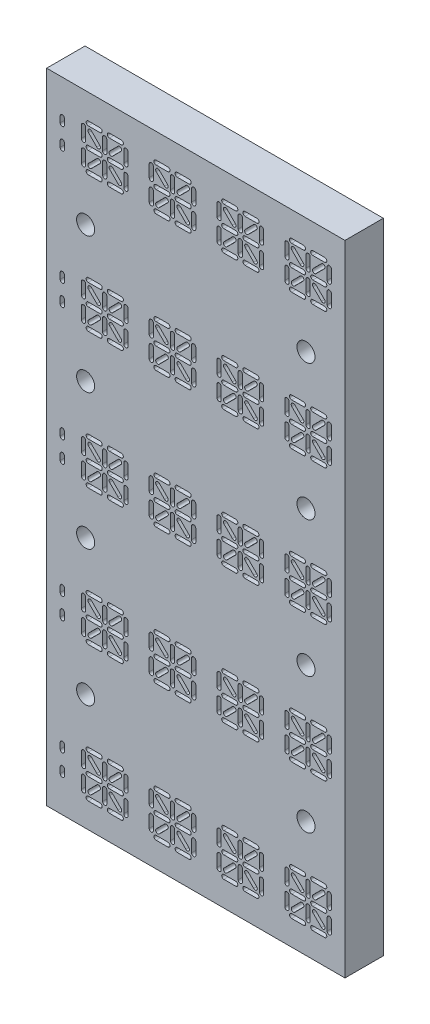
SolidWorks part; units mm, degrees
material "ABS PC"
ref_plane "Front Plane" through (0, 0, 0) normal (0, 0, 1) x (1, 0, 0)
ref_plane "Top Plane" through (0, 0, 0) normal (0, 1, 0) x (1, 0, 0)
ref_plane "Right Plane" through (0, 0, 0) normal (1, 0, 0) x (0, 0, -1)
sketch "Sketch1" plane through (0, 0, 0) normal (0, 0, 1) x (1, 0, 0)
  line L0 (265.9975, 197.0179) -> (342.1693, 194.9479) construction
  line L1 (297.418, 228.3826) -> (298.307, 228.3826) construction
  line L2 (297.418, 228.3826) -> (300.593, 228.3826) construction
  line L3 (302.371, 228.3826) -> (302.371, 231.5576) construction
  line L4 (296.7097, 229.0811) -> (296.7097, 229.9701) construction
  line L5 (296.7097, 230.8591) -> (296.7097, 234.0341) construction
  line L6 (296.7097, 234.0341) -> (299.8847, 234.0341) construction
  line L7 (296.7097, 234.0341) -> (297.0639, 234.3834) construction
  line L8 (296.7097, 234.0341) -> (297.418, 234.7326) construction
  line L9 (299.196, 231.5576) -> (300.593, 231.5576) construction
  line L10 (297.0639, 234.3834) -> (299.5404, 231.9069) construction
  line L11 (296.7097, 232.2561) -> (296.7097, 230.8591) construction
  line L12 (297.418, 231.5576) -> (296.7097, 231.5576) construction
  line L13 (299.8847, 232.2561) -> (299.196, 231.5576) construction
  line L14 (299.8945, 231.5576) -> (298.9307, 232.5165) construction
  line L15 (299.8945, 231.5576) -> (300.8534, 232.5214) construction
  line L16 (297.418, 234.7326) -> (307.578, 234.7326) construction
  line L17 (293.5347, 230.4146) -> (293.5347, 229.5256) construction
  line L18 (293.5347, 232.7006) -> (293.5347, 230.4146) construction
  line L19 (335.8892, 225.6039) -> (291.1852, 225.6039)
  line L20 (335.8892, 225.6039) -> (335.8892, 237.5114)
  line L21 (335.8892, 237.5114) -> (291.1852, 237.5114)
  line L22 (291.1852, 225.6039) -> (291.1852, 237.5114)
  line L23 (335.8892, 225.6039) -> (291.1852, 237.5114) construction
  line L24 (335.8892, 237.5114) -> (291.1852, 225.6039) construction
  line L25 (333.5397, 232.2561) -> (333.5397, 230.8591) construction
  line L26 (293.5347, 231.5576) -> (333.5397, 231.5576) construction
  line L27 (297.418, 228.3826) -> (299.196, 228.3826) construction
  line L32 (297.418, 228.7001) -> (299.196, 228.7001)
  line L33 (297.418, 228.0651) -> (299.196, 228.0651)
  line L34 (300.593, 228.3826) -> (302.371, 228.3826) construction
  line L35 (300.593, 228.7001) -> (302.371, 228.7001)
  line L36 (300.593, 228.0651) -> (302.371, 228.0651)
  line L37 (302.1155, 229.3415) -> (300.8582, 230.5987) construction
  line L38 (301.891, 229.117) -> (300.6337, 230.3742)
  line L39 (302.34, 229.566) -> (301.0827, 230.8233)
  line L40 (299.8847, 229.0811) -> (299.8847, 230.8591) construction
  line L41 (299.5672, 229.0811) -> (299.5672, 230.8591)
  line L42 (300.2022, 229.0811) -> (300.2022, 230.8591)
  line L43 (298.9356, 230.5939) -> (297.6784, 229.3366) construction
  line L44 (299.1601, 230.3694) -> (297.9029, 229.1121)
  line L45 (298.7111, 230.8184) -> (297.4539, 229.5611)
  line L46 (296.7097, 229.0811) -> (296.7097, 230.8591) construction
  line L47 (296.3922, 229.0811) -> (296.3922, 230.8591)
  line L48 (297.0272, 229.0811) -> (297.0272, 230.8591)
  line L49 (303.0597, 230.8591) -> (303.0597, 229.0811) construction
  line L50 (303.3772, 230.8591) -> (303.3772, 229.0811)
  line L51 (302.7422, 230.8591) -> (302.7422, 229.0811)
  line L52 (302.371, 231.5576) -> (300.593, 231.5576) construction
  line L53 (302.371, 231.2401) -> (300.593, 231.2401)
  line L54 (302.371, 231.8751) -> (300.593, 231.8751)
  line L55 (303.0597, 234.0341) -> (303.0597, 232.2561) construction
  line L56 (303.3772, 234.0341) -> (303.3772, 232.2561)
  line L57 (302.7422, 234.0341) -> (302.7422, 232.2561)
  line L58 (302.1106, 233.7786) -> (300.8534, 232.5214) construction
  line L59 (302.3351, 233.5541) -> (301.0779, 232.2969)
  line L60 (301.8861, 234.0031) -> (300.6289, 232.7459)
  line L61 (302.371, 234.7326) -> (300.593, 234.7326) construction
  line L62 (302.371, 234.4151) -> (300.593, 234.4151)
  line L63 (302.371, 235.0501) -> (300.593, 235.0501)
  line L64 (299.8847, 234.0341) -> (299.8847, 232.2561) construction
  line L65 (300.2022, 234.0341) -> (300.2022, 232.2561)
  line L66 (299.5672, 234.0341) -> (299.5672, 232.2561)
  line L67 (297.418, 231.5576) -> (299.196, 231.5576) construction
  line L68 (297.418, 231.8751) -> (299.196, 231.8751)
  line L69 (297.418, 231.2401) -> (299.196, 231.2401)
  line L70 (298.9307, 232.5165) -> (297.6735, 233.7737) construction
  line L71 (298.7062, 232.292) -> (297.449, 233.5492)
  line L72 (299.1552, 232.741) -> (297.898, 233.9983)
  line L73 (296.7097, 232.2561) -> (296.7097, 234.0341) construction
  line L74 (296.3922, 232.2561) -> (296.3922, 234.0341)
  line L75 (297.0272, 232.2561) -> (297.0272, 234.0341)
  line L76 (297.418, 234.7326) -> (299.196, 234.7326) construction
  line L77 (297.418, 235.0501) -> (299.196, 235.0501)
  line L78 (297.418, 234.4151) -> (299.196, 234.4151)
  line L79 (293.5347, 232.7006) -> (293.5347, 233.5896) construction
  line L80 (293.2172, 232.7006) -> (293.2172, 233.5896)
  line L81 (293.8522, 232.7006) -> (293.8522, 233.5896)
  line L82 (293.5347, 230.4146) -> (293.5347, 229.5256) construction
  line L83 (293.8522, 230.4146) -> (293.8522, 229.5256)
  line L84 (293.2172, 230.4146) -> (293.2172, 229.5256)
  line L85 (307.578, 228.3826) -> (309.356, 228.3826) construction
  line L86 (307.578, 228.7001) -> (309.356, 228.7001)
  line L87 (307.578, 228.0651) -> (309.356, 228.0651)
  line L88 (310.753, 228.3826) -> (312.531, 228.3826) construction
  line L89 (310.753, 228.7001) -> (312.531, 228.7001)
  line L90 (310.753, 228.0651) -> (312.531, 228.0651)
  line L91 (312.2755, 229.3415) -> (311.0182, 230.5987) construction
  line L92 (312.051, 229.117) -> (310.7937, 230.3742)
  line L93 (312.5, 229.566) -> (311.2427, 230.8233)
  line L94 (310.0447, 229.0811) -> (310.0447, 230.8591) construction
  line L95 (309.7272, 229.0811) -> (309.7272, 230.8591)
  line L96 (310.3622, 229.0811) -> (310.3622, 230.8591)
  line L97 (309.0956, 230.5939) -> (307.8384, 229.3366) construction
  line L98 (309.3201, 230.3694) -> (308.0629, 229.1121)
  line L99 (308.8711, 230.8184) -> (307.6139, 229.5611)
  line L100 (306.8697, 229.0811) -> (306.8697, 230.8591) construction
  line L101 (306.5522, 229.0811) -> (306.5522, 230.8591)
  line L102 (307.1872, 229.0811) -> (307.1872, 230.8591)
  line L103 (313.2197, 230.8591) -> (313.2197, 229.0811) construction
  line L104 (313.5372, 230.8591) -> (313.5372, 229.0811)
  line L105 (312.9022, 230.8591) -> (312.9022, 229.0811)
  line L106 (312.531, 231.5576) -> (310.753, 231.5576) construction
  line L107 (312.531, 231.2401) -> (310.753, 231.2401)
  line L108 (312.531, 231.8751) -> (310.753, 231.8751)
  line L109 (313.2197, 234.0341) -> (313.2197, 232.2561) construction
  line L110 (313.5372, 234.0341) -> (313.5372, 232.2561)
  line L111 (312.9022, 234.0341) -> (312.9022, 232.2561)
  line L112 (312.2706, 233.7786) -> (311.0134, 232.5214) construction
  line L113 (312.4951, 233.5541) -> (311.2379, 232.2969)
  line L114 (312.0461, 234.0031) -> (310.7889, 232.7459)
  line L115 (312.531, 234.7326) -> (310.753, 234.7326) construction
  line L116 (312.531, 234.4151) -> (310.753, 234.4151)
  line L117 (312.531, 235.0501) -> (310.753, 235.0501)
  line L118 (310.0447, 234.0341) -> (310.0447, 232.2561) construction
  line L119 (310.3622, 234.0341) -> (310.3622, 232.2561)
  line L120 (309.7272, 234.0341) -> (309.7272, 232.2561)
  line L121 (307.578, 231.5576) -> (309.356, 231.5576) construction
  line L122 (307.578, 231.8751) -> (309.356, 231.8751)
  line L123 (307.578, 231.2401) -> (309.356, 231.2401)
  line L124 (309.0907, 232.5165) -> (307.8335, 233.7737) construction
  line L125 (308.8662, 232.292) -> (307.609, 233.5492)
  line L126 (309.3152, 232.741) -> (308.058, 233.9983)
  line L127 (306.8697, 232.2561) -> (306.8697, 234.0341) construction
  line L128 (306.5522, 232.2561) -> (306.5522, 234.0341)
  line L129 (307.1872, 232.2561) -> (307.1872, 234.0341)
  line L130 (307.578, 234.7326) -> (309.356, 234.7326) construction
  line L131 (307.578, 235.0501) -> (309.356, 235.0501)
  line L132 (307.578, 234.4151) -> (309.356, 234.4151)
  line L133 (317.738, 228.3826) -> (319.516, 228.3826) construction
  line L134 (317.738, 228.7001) -> (319.516, 228.7001)
  line L135 (317.738, 228.0651) -> (319.516, 228.0651)
  line L136 (320.913, 228.3826) -> (322.691, 228.3826) construction
  line L137 (320.913, 228.7001) -> (322.691, 228.7001)
  line L138 (320.913, 228.0651) -> (322.691, 228.0651)
  line L139 (322.4355, 229.3415) -> (321.1782, 230.5987) construction
  line L140 (322.211, 229.117) -> (320.9537, 230.3742)
  line L141 (322.66, 229.566) -> (321.4027, 230.8233)
  line L142 (320.2047, 229.0811) -> (320.2047, 230.8591) construction
  line L143 (319.8872, 229.0811) -> (319.8872, 230.8591)
  line L144 (320.5222, 229.0811) -> (320.5222, 230.8591)
  line L145 (319.2556, 230.5939) -> (317.9984, 229.3366) construction
  line L146 (319.4801, 230.3694) -> (318.2229, 229.1121)
  line L147 (319.0311, 230.8184) -> (317.7739, 229.5611)
  line L148 (317.0297, 229.0811) -> (317.0297, 230.8591) construction
  line L149 (316.7122, 229.0811) -> (316.7122, 230.8591)
  line L150 (317.3472, 229.0811) -> (317.3472, 230.8591)
  line L151 (323.3797, 230.8591) -> (323.3797, 229.0811) construction
  line L152 (323.6972, 230.8591) -> (323.6972, 229.0811)
  line L153 (323.0622, 230.8591) -> (323.0622, 229.0811)
  line L154 (322.691, 231.5576) -> (320.913, 231.5576) construction
  line L155 (322.691, 231.2401) -> (320.913, 231.2401)
  line L156 (322.691, 231.8751) -> (320.913, 231.8751)
  line L157 (323.3797, 234.0341) -> (323.3797, 232.2561) construction
  line L158 (323.6972, 234.0341) -> (323.6972, 232.2561)
  line L159 (323.0622, 234.0341) -> (323.0622, 232.2561)
  line L160 (322.4306, 233.7786) -> (321.1734, 232.5214) construction
  line L161 (322.6551, 233.5541) -> (321.3979, 232.2969)
  line L162 (322.2061, 234.0031) -> (320.9489, 232.7459)
  line L163 (322.691, 234.7326) -> (320.913, 234.7326) construction
  line L164 (322.691, 234.4151) -> (320.913, 234.4151)
  line L165 (322.691, 235.0501) -> (320.913, 235.0501)
  line L166 (320.2047, 234.0341) -> (320.2047, 232.2561) construction
  line L167 (320.5222, 234.0341) -> (320.5222, 232.2561)
  line L168 (319.8872, 234.0341) -> (319.8872, 232.2561)
  line L169 (317.738, 231.5576) -> (319.516, 231.5576) construction
  line L170 (317.738, 231.8751) -> (319.516, 231.8751)
  line L171 (317.738, 231.2401) -> (319.516, 231.2401)
  line L172 (319.2507, 232.5165) -> (317.9935, 233.7737) construction
  line L173 (319.0262, 232.292) -> (317.769, 233.5492)
  line L174 (319.4752, 232.741) -> (318.218, 233.9983)
  line L175 (317.0297, 232.2561) -> (317.0297, 234.0341) construction
  line L176 (316.7122, 232.2561) -> (316.7122, 234.0341)
  line L177 (317.3472, 232.2561) -> (317.3472, 234.0341)
  line L178 (317.738, 234.7326) -> (319.516, 234.7326) construction
  line L179 (317.738, 235.0501) -> (319.516, 235.0501)
  line L180 (317.738, 234.4151) -> (319.516, 234.4151)
  line L181 (327.898, 228.3826) -> (329.676, 228.3826) construction
  line L182 (327.898, 228.7001) -> (329.676, 228.7001)
  line L183 (327.898, 228.0651) -> (329.676, 228.0651)
  line L184 (331.073, 228.3826) -> (332.851, 228.3826) construction
  line L185 (331.073, 228.7001) -> (332.851, 228.7001)
  line L186 (331.073, 228.0651) -> (332.851, 228.0651)
  line L187 (332.5955, 229.3415) -> (331.3382, 230.5987) construction
  line L188 (332.371, 229.117) -> (331.1137, 230.3742)
  line L189 (332.82, 229.566) -> (331.5627, 230.8233)
  line L190 (330.3647, 229.0811) -> (330.3647, 230.8591) construction
  line L191 (330.0472, 229.0811) -> (330.0472, 230.8591)
  line L192 (330.6822, 229.0811) -> (330.6822, 230.8591)
  line L193 (329.4156, 230.5939) -> (328.1584, 229.3366) construction
  line L194 (329.6401, 230.3694) -> (328.3829, 229.1121)
  line L195 (329.1911, 230.8184) -> (327.9339, 229.5611)
  line L196 (327.1897, 229.0811) -> (327.1897, 230.8591) construction
  line L197 (326.8722, 229.0811) -> (326.8722, 230.8591)
  line L198 (327.5072, 229.0811) -> (327.5072, 230.8591)
  line L199 (333.5397, 230.8591) -> (333.5397, 229.0811) construction
  line L200 (333.8572, 230.8591) -> (333.8572, 229.0811)
  line L201 (333.2222, 230.8591) -> (333.2222, 229.0811)
  line L202 (332.851, 231.5576) -> (331.073, 231.5576) construction
  line L203 (332.851, 231.2401) -> (331.073, 231.2401)
  line L204 (332.851, 231.8751) -> (331.073, 231.8751)
  line L205 (333.5397, 234.0341) -> (333.5397, 232.2561) construction
  line L206 (333.8572, 234.0341) -> (333.8572, 232.2561)
  line L207 (333.2222, 234.0341) -> (333.2222, 232.2561)
  line L208 (332.5906, 233.7786) -> (331.3334, 232.5214) construction
  line L209 (332.8151, 233.5541) -> (331.5579, 232.2969)
  line L210 (332.3661, 234.0031) -> (331.1089, 232.7459)
  line L211 (332.851, 234.7326) -> (331.073, 234.7326) construction
  line L212 (332.851, 234.4151) -> (331.073, 234.4151)
  line L213 (332.851, 235.0501) -> (331.073, 235.0501)
  line L214 (330.3647, 234.0341) -> (330.3647, 232.2561) construction
  line L215 (330.6822, 234.0341) -> (330.6822, 232.2561)
  line L216 (330.0472, 234.0341) -> (330.0472, 232.2561)
  line L217 (327.898, 231.5576) -> (329.676, 231.5576) construction
  line L218 (327.898, 231.8751) -> (329.676, 231.8751)
  line L219 (327.898, 231.2401) -> (329.676, 231.2401)
  line L220 (329.4107, 232.5165) -> (328.1535, 233.7737) construction
  line L221 (329.1862, 232.292) -> (327.929, 233.5492)
  line L222 (329.6352, 232.741) -> (328.378, 233.9983)
  line L223 (327.1897, 232.2561) -> (327.1897, 234.0341) construction
  line L224 (326.8722, 232.2561) -> (326.8722, 234.0341)
  line L225 (327.5072, 232.2561) -> (327.5072, 234.0341)
  line L226 (327.898, 234.7326) -> (329.676, 234.7326) construction
  line L227 (327.898, 235.0501) -> (329.676, 235.0501)
  line L228 (327.898, 234.4151) -> (329.676, 234.4151)
  line L229 (296.7097, 229.0811) -> (306.8697, 229.0811) construction
  circle A0 centre (297.418, 228.3826) radius 0.3175 construction
  circle A3 centre (298.307, 228.3826) radius 0.3175 construction
  circle A4 centre (299.196, 228.3826) radius 0.3175 construction
  circle A5 centre (300.593, 228.3826) radius 0.3175 construction
  circle A6 centre (301.482, 228.3826) radius 0.3175 construction
  circle A7 centre (302.371, 228.3826) radius 0.3175 construction
  circle A8 centre (302.371, 231.5576) radius 0.3175 construction
  circle A9 centre (301.482, 231.5576) radius 0.3175 construction
  circle A10 centre (300.593, 231.5576) radius 0.3175 construction
  circle A11 centre (299.196, 231.5576) radius 0.3175 construction
  circle A12 centre (298.307, 231.5576) radius 0.3175 construction
  circle A13 centre (297.418, 231.5576) radius 0.3175 construction
  circle A14 centre (302.371, 234.7326) radius 0.3175 construction
  circle A15 centre (301.482, 234.7326) radius 0.3175 construction
  circle A16 centre (300.593, 234.7326) radius 0.3175 construction
  circle A17 centre (299.196, 234.7326) radius 0.3175 construction
  circle A18 centre (298.307, 234.7326) radius 0.3175 construction
  circle A19 centre (297.418, 234.7326) radius 0.3175 construction
  circle A20 centre (296.7097, 229.0811) radius 0.3175 construction
  circle A21 centre (296.7097, 229.9701) radius 0.3175 construction
  circle A22 centre (296.7097, 230.8591) radius 0.3175 construction
  circle A23 centre (296.7097, 234.0341) radius 0.3175 construction
  circle A24 centre (296.7097, 233.1451) radius 0.3175 construction
  circle A25 centre (296.7097, 232.2561) radius 0.3175 construction
  circle A26 centre (299.8847, 234.0341) radius 0.3175 construction
  circle A27 centre (299.8847, 233.1451) radius 0.3175 construction
  circle A28 centre (299.8847, 232.2561) radius 0.3175 construction
  circle A29 centre (299.8847, 230.8591) radius 0.3175 construction
  circle A30 centre (299.8847, 229.9701) radius 0.3175 construction
  circle A31 centre (299.8847, 229.0811) radius 0.3175 construction
  circle A32 centre (297.6735, 233.7737) radius 0.3175 construction
  circle A33 centre (298.3021, 233.1451) radius 0.3175 construction
  circle A34 centre (298.9307, 232.5165) radius 0.3175 construction
  circle A35 centre (303.0597, 234.0341) radius 0.3175 construction
  circle A36 centre (303.0597, 233.1451) radius 0.3175 construction
  circle A37 centre (303.0597, 232.2561) radius 0.3175 construction
  circle A38 centre (303.0597, 230.8591) radius 0.3175 construction
  circle A39 centre (303.0597, 229.9701) radius 0.3175 construction
  circle A40 centre (303.0597, 229.0811) radius 0.3175 construction
  circle A41 centre (300.8534, 232.5214) radius 0.3175 construction
  circle A42 centre (301.482, 233.15) radius 0.3175 construction
  circle A43 centre (302.1106, 233.7786) radius 0.3175 construction
  circle A44 centre (300.8582, 230.5987) radius 0.3175 construction
  circle A45 centre (301.4869, 229.9701) radius 0.3175 construction
  circle A46 centre (302.1155, 229.3415) radius 0.3175 construction
  circle A47 centre (298.9356, 230.5939) radius 0.3175 construction
  circle A48 centre (298.307, 229.9653) radius 0.3175 construction
  circle A49 centre (297.6784, 229.3366) radius 0.3175 construction
  circle A50 centre (307.578, 234.7326) radius 0.3175 construction
  circle A51 centre (306.8697, 234.0341) radius 0.3175 construction
  circle A52 centre (306.8697, 233.1451) radius 0.3175 construction
  circle A53 centre (306.8697, 232.2561) radius 0.3175 construction
  circle A54 centre (308.467, 234.7326) radius 0.3175 construction
  circle A55 centre (309.356, 234.7326) radius 0.3175 construction
  circle A56 centre (310.753, 234.7326) radius 0.3175 construction
  circle A57 centre (311.642, 234.7326) radius 0.3175 construction
  circle A58 centre (312.531, 234.7326) radius 0.3175 construction
  circle A59 centre (313.2197, 234.0341) radius 0.3175 construction
  circle A60 centre (313.2197, 233.1451) radius 0.3175 construction
  circle A61 centre (313.2197, 232.2561) radius 0.3175 construction
  circle A62 centre (313.2197, 230.8591) radius 0.3175 construction
  circle A63 centre (313.2197, 229.9701) radius 0.3175 construction
  circle A64 centre (313.2197, 229.0811) radius 0.3175 construction
  circle A65 centre (312.531, 228.3826) radius 0.3175 construction
  circle A66 centre (311.642, 228.3826) radius 0.3175 construction
  circle A67 centre (310.753, 228.3826) radius 0.3175 construction
  circle A68 centre (309.356, 228.3826) radius 0.3175 construction
  circle A69 centre (308.467, 228.3826) radius 0.3175 construction
  circle A70 centre (307.578, 228.3826) radius 0.3175 construction
  circle A71 centre (306.8697, 229.0811) radius 0.3175 construction
  circle A72 centre (306.8697, 229.9701) radius 0.3175 construction
  circle A73 centre (306.8697, 230.8591) radius 0.3175 construction
  circle A74 centre (307.578, 231.5576) radius 0.3175 construction
  circle A75 centre (308.467, 231.5576) radius 0.3175 construction
  circle A76 centre (309.356, 231.5576) radius 0.3175 construction
  circle A77 centre (310.753, 231.5576) radius 0.3175 construction
  circle A78 centre (311.642, 231.5576) radius 0.3175 construction
  circle A79 centre (312.531, 231.5576) radius 0.3175 construction
  circle A80 centre (312.2706, 233.7786) radius 0.3175 construction
  circle A81 centre (311.642, 233.15) radius 0.3175 construction
  circle A82 centre (311.0134, 232.5214) radius 0.3175 construction
  circle A83 centre (310.0447, 232.2561) radius 0.3175 construction
  circle A84 centre (310.0447, 233.1451) radius 0.3175 construction
  circle A85 centre (310.0447, 234.0341) radius 0.3175 construction
  circle A86 centre (309.0907, 232.5165) radius 0.3175 construction
  circle A87 centre (308.4621, 233.1451) radius 0.3175 construction
  circle A88 centre (307.8335, 233.7737) radius 0.3175 construction
  circle A89 centre (307.8384, 229.3366) radius 0.3175 construction
  circle A90 centre (308.467, 229.9653) radius 0.3175 construction
  circle A91 centre (309.0956, 230.5939) radius 0.3175 construction
  circle A92 centre (310.0447, 230.8591) radius 0.3175 construction
  circle A93 centre (310.0447, 229.9701) radius 0.3175 construction
  circle A94 centre (310.0447, 229.0811) radius 0.3175 construction
  circle A95 centre (312.2755, 229.3415) radius 0.3175 construction
  circle A96 centre (311.6469, 229.9701) radius 0.3175 construction
  circle A97 centre (311.0182, 230.5987) radius 0.3175 construction
  circle A98 centre (317.738, 234.7326) radius 0.3175 construction
  circle A99 centre (317.0297, 234.0341) radius 0.3175 construction
  circle A100 centre (317.0297, 233.1451) radius 0.3175 construction
  circle A101 centre (317.0297, 232.2561) radius 0.3175 construction
  circle A102 centre (318.627, 234.7326) radius 0.3175 construction
  circle A103 centre (319.516, 234.7326) radius 0.3175 construction
  circle A104 centre (320.913, 234.7326) radius 0.3175 construction
  circle A105 centre (321.802, 234.7326) radius 0.3175 construction
  circle A106 centre (322.691, 234.7326) radius 0.3175 construction
  circle A107 centre (323.3797, 234.0341) radius 0.3175 construction
  circle A108 centre (323.3797, 233.1451) radius 0.3175 construction
  circle A109 centre (323.3797, 232.2561) radius 0.3175 construction
  circle A110 centre (323.3797, 230.8591) radius 0.3175 construction
  circle A111 centre (323.3797, 229.9701) radius 0.3175 construction
  circle A112 centre (323.3797, 229.0811) radius 0.3175 construction
  circle A113 centre (322.691, 228.3826) radius 0.3175 construction
  circle A114 centre (321.802, 228.3826) radius 0.3175 construction
  circle A115 centre (320.913, 228.3826) radius 0.3175 construction
  circle A116 centre (319.516, 228.3826) radius 0.3175 construction
  circle A117 centre (318.627, 228.3826) radius 0.3175 construction
  circle A118 centre (317.738, 228.3826) radius 0.3175 construction
  circle A119 centre (317.0297, 229.0811) radius 0.3175 construction
  circle A120 centre (317.0297, 229.9701) radius 0.3175 construction
  circle A121 centre (317.0297, 230.8591) radius 0.3175 construction
  circle A122 centre (317.738, 231.5576) radius 0.3175 construction
  circle A123 centre (318.627, 231.5576) radius 0.3175 construction
  circle A124 centre (319.516, 231.5576) radius 0.3175 construction
  circle A125 centre (320.913, 231.5576) radius 0.3175 construction
  circle A126 centre (321.802, 231.5576) radius 0.3175 construction
  circle A127 centre (322.691, 231.5576) radius 0.3175 construction
  circle A128 centre (322.4306, 233.7786) radius 0.3175 construction
  circle A129 centre (321.802, 233.15) radius 0.3175 construction
  circle A130 centre (321.1734, 232.5214) radius 0.3175 construction
  circle A131 centre (320.2047, 232.2561) radius 0.3175 construction
  circle A132 centre (320.2047, 233.1451) radius 0.3175 construction
  circle A133 centre (320.2047, 234.0341) radius 0.3175 construction
  circle A134 centre (319.2507, 232.5165) radius 0.3175 construction
  circle A135 centre (318.6221, 233.1451) radius 0.3175 construction
  circle A136 centre (317.9935, 233.7737) radius 0.3175 construction
  circle A137 centre (317.9984, 229.3366) radius 0.3175 construction
  circle A138 centre (318.627, 229.9653) radius 0.3175 construction
  circle A139 centre (319.2556, 230.5939) radius 0.3175 construction
  circle A140 centre (320.2047, 230.8591) radius 0.3175 construction
  circle A141 centre (320.2047, 229.9701) radius 0.3175 construction
  circle A142 centre (320.2047, 229.0811) radius 0.3175 construction
  circle A143 centre (322.4355, 229.3415) radius 0.3175 construction
  circle A144 centre (321.8069, 229.9701) radius 0.3175 construction
  circle A145 centre (321.1782, 230.5987) radius 0.3175 construction
  circle A146 centre (327.898, 234.7326) radius 0.3175 construction
  circle A147 centre (327.1897, 234.0341) radius 0.3175 construction
  circle A148 centre (327.1897, 233.1451) radius 0.3175 construction
  circle A149 centre (327.1897, 232.2561) radius 0.3175 construction
  circle A150 centre (328.787, 234.7326) radius 0.3175 construction
  circle A151 centre (329.676, 234.7326) radius 0.3175 construction
  circle A152 centre (331.073, 234.7326) radius 0.3175 construction
  circle A153 centre (331.962, 234.7326) radius 0.3175 construction
  circle A154 centre (332.851, 234.7326) radius 0.3175 construction
  circle A155 centre (333.5397, 234.0341) radius 0.3175 construction
  circle A156 centre (333.5397, 233.1451) radius 0.3175 construction
  circle A157 centre (333.5397, 232.2561) radius 0.3175 construction
  circle A158 centre (333.5397, 230.8591) radius 0.3175 construction
  circle A159 centre (333.5397, 229.9701) radius 0.3175 construction
  circle A160 centre (333.5397, 229.0811) radius 0.3175 construction
  circle A161 centre (332.851, 228.3826) radius 0.3175 construction
  circle A162 centre (331.962, 228.3826) radius 0.3175 construction
  circle A163 centre (331.073, 228.3826) radius 0.3175 construction
  circle A164 centre (329.676, 228.3826) radius 0.3175 construction
  circle A165 centre (328.787, 228.3826) radius 0.3175 construction
  circle A166 centre (327.898, 228.3826) radius 0.3175 construction
  circle A167 centre (327.1897, 229.0811) radius 0.3175 construction
  circle A168 centre (327.1897, 229.9701) radius 0.3175 construction
  circle A169 centre (327.1897, 230.8591) radius 0.3175 construction
  circle A170 centre (327.898, 231.5576) radius 0.3175 construction
  circle A171 centre (328.787, 231.5576) radius 0.3175 construction
  circle A172 centre (329.676, 231.5576) radius 0.3175 construction
  circle A173 centre (331.073, 231.5576) radius 0.3175 construction
  circle A174 centre (331.962, 231.5576) radius 0.3175 construction
  circle A175 centre (332.851, 231.5576) radius 0.3175 construction
  circle A176 centre (332.5906, 233.7786) radius 0.3175 construction
  circle A177 centre (331.962, 233.15) radius 0.3175 construction
  circle A178 centre (331.3334, 232.5214) radius 0.3175 construction
  circle A179 centre (330.3647, 232.2561) radius 0.3175 construction
  circle A180 centre (330.3647, 233.1451) radius 0.3175 construction
  circle A181 centre (330.3647, 234.0341) radius 0.3175 construction
  circle A182 centre (329.4107, 232.5165) radius 0.3175 construction
  circle A183 centre (328.7821, 233.1451) radius 0.3175 construction
  circle A184 centre (328.1535, 233.7737) radius 0.3175 construction
  circle A185 centre (328.1584, 229.3366) radius 0.3175 construction
  circle A186 centre (328.787, 229.9653) radius 0.3175 construction
  circle A187 centre (329.4156, 230.5939) radius 0.3175 construction
  circle A188 centre (330.3647, 230.8591) radius 0.3175 construction
  circle A189 centre (330.3647, 229.9701) radius 0.3175 construction
  circle A190 centre (330.3647, 229.0811) radius 0.3175 construction
  circle A191 centre (332.5955, 229.3415) radius 0.3175 construction
  circle A192 centre (331.9669, 229.9701) radius 0.3175 construction
  circle A193 centre (331.3382, 230.5987) radius 0.3175 construction
  circle A194 centre (293.5347, 229.5256) radius 0.3175 construction
  circle A195 centre (293.5347, 230.4146) radius 0.3175 construction
  circle A196 centre (293.5347, 233.5896) radius 0.3175 construction
  circle A197 centre (293.5347, 232.7006) radius 0.3175 construction
  arc A198 (297.418, 228.7001) -> (297.418, 228.0651) centre (297.418, 228.3826) ccw
  arc A199 (299.196, 228.0651) -> (299.196, 228.7001) centre (299.196, 228.3826) ccw
  arc A200 (300.593, 228.7001) -> (300.593, 228.0651) centre (300.593, 228.3826) ccw
  arc A201 (302.371, 228.0651) -> (302.371, 228.7001) centre (302.371, 228.3826) ccw
  arc A202 (301.891, 229.117) -> (302.34, 229.566) centre (302.1155, 229.3415) ccw
  arc A203 (301.0827, 230.8233) -> (300.6337, 230.3742) centre (300.8582, 230.5987) ccw
  arc A204 (299.5672, 229.0811) -> (300.2022, 229.0811) centre (299.8847, 229.0811) ccw
  arc A205 (300.2022, 230.8591) -> (299.5672, 230.8591) centre (299.8847, 230.8591) ccw
  arc A206 (299.1601, 230.3694) -> (298.7111, 230.8184) centre (298.9356, 230.5939) ccw
  arc A207 (297.4539, 229.5611) -> (297.9029, 229.1121) centre (297.6784, 229.3366) ccw
  arc A208 (296.3922, 229.0811) -> (297.0272, 229.0811) centre (296.7097, 229.0811) ccw
  arc A209 (297.0272, 230.8591) -> (296.3922, 230.8591) centre (296.7097, 230.8591) ccw
  arc A210 (303.3772, 230.8591) -> (302.7422, 230.8591) centre (303.0597, 230.8591) ccw
  arc A211 (302.7422, 229.0811) -> (303.3772, 229.0811) centre (303.0597, 229.0811) ccw
  arc A212 (302.371, 231.2401) -> (302.371, 231.8751) centre (302.371, 231.5576) ccw
  arc A213 (300.593, 231.8751) -> (300.593, 231.2401) centre (300.593, 231.5576) ccw
  arc A214 (303.3772, 234.0341) -> (302.7422, 234.0341) centre (303.0597, 234.0341) ccw
  arc A215 (302.7422, 232.2561) -> (303.3772, 232.2561) centre (303.0597, 232.2561) ccw
  arc A216 (302.3351, 233.5541) -> (301.8861, 234.0031) centre (302.1106, 233.7786) ccw
  arc A217 (300.6289, 232.7459) -> (301.0779, 232.2969) centre (300.8534, 232.5214) ccw
  arc A218 (302.371, 234.4151) -> (302.371, 235.0501) centre (302.371, 234.7326) ccw
  arc A219 (300.593, 235.0501) -> (300.593, 234.4151) centre (300.593, 234.7326) ccw
  arc A220 (300.2022, 234.0341) -> (299.5672, 234.0341) centre (299.8847, 234.0341) ccw
  arc A221 (299.5672, 232.2561) -> (300.2022, 232.2561) centre (299.8847, 232.2561) ccw
  arc A222 (297.418, 231.8751) -> (297.418, 231.2401) centre (297.418, 231.5576) ccw
  arc A223 (299.196, 231.2401) -> (299.196, 231.8751) centre (299.196, 231.5576) ccw
  arc A224 (298.7062, 232.292) -> (299.1552, 232.741) centre (298.9307, 232.5165) ccw
  arc A225 (297.898, 233.9983) -> (297.449, 233.5492) centre (297.6735, 233.7737) ccw
  arc A226 (296.3922, 232.2561) -> (297.0272, 232.2561) centre (296.7097, 232.2561) ccw
  arc A227 (297.0272, 234.0341) -> (296.3922, 234.0341) centre (296.7097, 234.0341) ccw
  arc A228 (297.418, 235.0501) -> (297.418, 234.4151) centre (297.418, 234.7326) ccw
  arc A229 (299.196, 234.4151) -> (299.196, 235.0501) centre (299.196, 234.7326) ccw
  arc A230 (293.2172, 232.7006) -> (293.8522, 232.7006) centre (293.5347, 232.7006) ccw
  arc A231 (293.8522, 233.5896) -> (293.2172, 233.5896) centre (293.5347, 233.5896) ccw
  arc A232 (293.8522, 230.4146) -> (293.2172, 230.4146) centre (293.5347, 230.4146) ccw
  arc A233 (293.2172, 229.5256) -> (293.8522, 229.5256) centre (293.5347, 229.5256) ccw
  arc A234 (307.578, 228.7001) -> (307.578, 228.0651) centre (307.578, 228.3826) ccw
  arc A235 (309.356, 228.0651) -> (309.356, 228.7001) centre (309.356, 228.3826) ccw
  arc A236 (310.753, 228.7001) -> (310.753, 228.0651) centre (310.753, 228.3826) ccw
  arc A237 (312.531, 228.0651) -> (312.531, 228.7001) centre (312.531, 228.3826) ccw
  arc A238 (312.051, 229.117) -> (312.5, 229.566) centre (312.2755, 229.3415) ccw
  arc A239 (311.2427, 230.8233) -> (310.7937, 230.3742) centre (311.0182, 230.5987) ccw
  arc A240 (309.7272, 229.0811) -> (310.3622, 229.0811) centre (310.0447, 229.0811) ccw
  arc A241 (310.3622, 230.8591) -> (309.7272, 230.8591) centre (310.0447, 230.8591) ccw
  arc A242 (309.3201, 230.3694) -> (308.8711, 230.8184) centre (309.0956, 230.5939) ccw
  arc A243 (307.6139, 229.5611) -> (308.0629, 229.1121) centre (307.8384, 229.3366) ccw
  arc A244 (306.5522, 229.0811) -> (307.1872, 229.0811) centre (306.8697, 229.0811) ccw
  arc A245 (307.1872, 230.8591) -> (306.5522, 230.8591) centre (306.8697, 230.8591) ccw
  arc A246 (313.5372, 230.8591) -> (312.9022, 230.8591) centre (313.2197, 230.8591) ccw
  arc A247 (312.9022, 229.0811) -> (313.5372, 229.0811) centre (313.2197, 229.0811) ccw
  arc A248 (312.531, 231.2401) -> (312.531, 231.8751) centre (312.531, 231.5576) ccw
  arc A249 (310.753, 231.8751) -> (310.753, 231.2401) centre (310.753, 231.5576) ccw
  arc A250 (313.5372, 234.0341) -> (312.9022, 234.0341) centre (313.2197, 234.0341) ccw
  arc A251 (312.9022, 232.2561) -> (313.5372, 232.2561) centre (313.2197, 232.2561) ccw
  arc A252 (312.4951, 233.5541) -> (312.0461, 234.0031) centre (312.2706, 233.7786) ccw
  arc A253 (310.7889, 232.7459) -> (311.2379, 232.2969) centre (311.0134, 232.5214) ccw
  arc A254 (312.531, 234.4151) -> (312.531, 235.0501) centre (312.531, 234.7326) ccw
  arc A255 (310.753, 235.0501) -> (310.753, 234.4151) centre (310.753, 234.7326) ccw
  arc A256 (310.3622, 234.0341) -> (309.7272, 234.0341) centre (310.0447, 234.0341) ccw
  arc A257 (309.7272, 232.2561) -> (310.3622, 232.2561) centre (310.0447, 232.2561) ccw
  arc A258 (307.578, 231.8751) -> (307.578, 231.2401) centre (307.578, 231.5576) ccw
  arc A259 (309.356, 231.2401) -> (309.356, 231.8751) centre (309.356, 231.5576) ccw
  arc A260 (308.8662, 232.292) -> (309.3152, 232.741) centre (309.0907, 232.5165) ccw
  arc A261 (308.058, 233.9983) -> (307.609, 233.5492) centre (307.8335, 233.7737) ccw
  arc A262 (306.5522, 232.2561) -> (307.1872, 232.2561) centre (306.8697, 232.2561) ccw
  arc A263 (307.1872, 234.0341) -> (306.5522, 234.0341) centre (306.8697, 234.0341) ccw
  arc A264 (307.578, 235.0501) -> (307.578, 234.4151) centre (307.578, 234.7326) ccw
  arc A265 (309.356, 234.4151) -> (309.356, 235.0501) centre (309.356, 234.7326) ccw
  arc A266 (317.738, 228.7001) -> (317.738, 228.0651) centre (317.738, 228.3826) ccw
  arc A267 (319.516, 228.0651) -> (319.516, 228.7001) centre (319.516, 228.3826) ccw
  arc A268 (320.913, 228.7001) -> (320.913, 228.0651) centre (320.913, 228.3826) ccw
  arc A269 (322.691, 228.0651) -> (322.691, 228.7001) centre (322.691, 228.3826) ccw
  arc A270 (322.211, 229.117) -> (322.66, 229.566) centre (322.4355, 229.3415) ccw
  arc A271 (321.4027, 230.8233) -> (320.9537, 230.3742) centre (321.1782, 230.5987) ccw
  arc A272 (319.8872, 229.0811) -> (320.5222, 229.0811) centre (320.2047, 229.0811) ccw
  arc A273 (320.5222, 230.8591) -> (319.8872, 230.8591) centre (320.2047, 230.8591) ccw
  arc A274 (319.4801, 230.3694) -> (319.0311, 230.8184) centre (319.2556, 230.5939) ccw
  arc A275 (317.7739, 229.5611) -> (318.2229, 229.1121) centre (317.9984, 229.3366) ccw
  arc A276 (316.7122, 229.0811) -> (317.3472, 229.0811) centre (317.0297, 229.0811) ccw
  arc A277 (317.3472, 230.8591) -> (316.7122, 230.8591) centre (317.0297, 230.8591) ccw
  arc A278 (323.6972, 230.8591) -> (323.0622, 230.8591) centre (323.3797, 230.8591) ccw
  arc A279 (323.0622, 229.0811) -> (323.6972, 229.0811) centre (323.3797, 229.0811) ccw
  arc A280 (322.691, 231.2401) -> (322.691, 231.8751) centre (322.691, 231.5576) ccw
  arc A281 (320.913, 231.8751) -> (320.913, 231.2401) centre (320.913, 231.5576) ccw
  arc A282 (323.6972, 234.0341) -> (323.0622, 234.0341) centre (323.3797, 234.0341) ccw
  arc A283 (323.0622, 232.2561) -> (323.6972, 232.2561) centre (323.3797, 232.2561) ccw
  arc A284 (322.6551, 233.5541) -> (322.2061, 234.0031) centre (322.4306, 233.7786) ccw
  arc A285 (320.9489, 232.7459) -> (321.3979, 232.2969) centre (321.1734, 232.5214) ccw
  arc A286 (322.691, 234.4151) -> (322.691, 235.0501) centre (322.691, 234.7326) ccw
  arc A287 (320.913, 235.0501) -> (320.913, 234.4151) centre (320.913, 234.7326) ccw
  arc A288 (320.5222, 234.0341) -> (319.8872, 234.0341) centre (320.2047, 234.0341) ccw
  arc A289 (319.8872, 232.2561) -> (320.5222, 232.2561) centre (320.2047, 232.2561) ccw
  arc A290 (317.738, 231.8751) -> (317.738, 231.2401) centre (317.738, 231.5576) ccw
  arc A291 (319.516, 231.2401) -> (319.516, 231.8751) centre (319.516, 231.5576) ccw
  arc A292 (319.0262, 232.292) -> (319.4752, 232.741) centre (319.2507, 232.5165) ccw
  arc A293 (318.218, 233.9983) -> (317.769, 233.5492) centre (317.9935, 233.7737) ccw
  arc A294 (316.7122, 232.2561) -> (317.3472, 232.2561) centre (317.0297, 232.2561) ccw
  arc A295 (317.3472, 234.0341) -> (316.7122, 234.0341) centre (317.0297, 234.0341) ccw
  arc A296 (317.738, 235.0501) -> (317.738, 234.4151) centre (317.738, 234.7326) ccw
  arc A297 (319.516, 234.4151) -> (319.516, 235.0501) centre (319.516, 234.7326) ccw
  arc A298 (327.898, 228.7001) -> (327.898, 228.0651) centre (327.898, 228.3826) ccw
  arc A299 (329.676, 228.0651) -> (329.676, 228.7001) centre (329.676, 228.3826) ccw
  arc A300 (331.073, 228.7001) -> (331.073, 228.0651) centre (331.073, 228.3826) ccw
  arc A301 (332.851, 228.0651) -> (332.851, 228.7001) centre (332.851, 228.3826) ccw
  arc A302 (332.371, 229.117) -> (332.82, 229.566) centre (332.5955, 229.3415) ccw
  arc A303 (331.5627, 230.8233) -> (331.1137, 230.3742) centre (331.3382, 230.5987) ccw
  arc A304 (330.0472, 229.0811) -> (330.6822, 229.0811) centre (330.3647, 229.0811) ccw
  arc A305 (330.6822, 230.8591) -> (330.0472, 230.8591) centre (330.3647, 230.8591) ccw
  arc A306 (329.6401, 230.3694) -> (329.1911, 230.8184) centre (329.4156, 230.5939) ccw
  arc A307 (327.9339, 229.5611) -> (328.3829, 229.1121) centre (328.1584, 229.3366) ccw
  arc A308 (326.8722, 229.0811) -> (327.5072, 229.0811) centre (327.1897, 229.0811) ccw
  arc A309 (327.5072, 230.8591) -> (326.8722, 230.8591) centre (327.1897, 230.8591) ccw
  arc A310 (333.8572, 230.8591) -> (333.2222, 230.8591) centre (333.5397, 230.8591) ccw
  arc A311 (333.2222, 229.0811) -> (333.8572, 229.0811) centre (333.5397, 229.0811) ccw
  arc A312 (332.851, 231.2401) -> (332.851, 231.8751) centre (332.851, 231.5576) ccw
  arc A313 (331.073, 231.8751) -> (331.073, 231.2401) centre (331.073, 231.5576) ccw
  arc A314 (333.8572, 234.0341) -> (333.2222, 234.0341) centre (333.5397, 234.0341) ccw
  arc A315 (333.2222, 232.2561) -> (333.8572, 232.2561) centre (333.5397, 232.2561) ccw
  arc A316 (332.8151, 233.5541) -> (332.3661, 234.0031) centre (332.5906, 233.7786) ccw
  arc A317 (331.1089, 232.7459) -> (331.5579, 232.2969) centre (331.3334, 232.5214) ccw
  arc A318 (332.851, 234.4151) -> (332.851, 235.0501) centre (332.851, 234.7326) ccw
  arc A319 (331.073, 235.0501) -> (331.073, 234.4151) centre (331.073, 234.7326) ccw
  arc A320 (330.6822, 234.0341) -> (330.0472, 234.0341) centre (330.3647, 234.0341) ccw
  arc A321 (330.0472, 232.2561) -> (330.6822, 232.2561) centre (330.3647, 232.2561) ccw
  arc A322 (327.898, 231.8751) -> (327.898, 231.2401) centre (327.898, 231.5576) ccw
  arc A323 (329.676, 231.2401) -> (329.676, 231.8751) centre (329.676, 231.5576) ccw
  arc A324 (329.1862, 232.292) -> (329.6352, 232.741) centre (329.4107, 232.5165) ccw
  arc A325 (328.378, 233.9983) -> (327.929, 233.5492) centre (328.1535, 233.7737) ccw
  arc A326 (326.8722, 232.2561) -> (327.5072, 232.2561) centre (327.1897, 232.2561) ccw
  arc A327 (327.5072, 234.0341) -> (326.8722, 234.0341) centre (327.1897, 234.0341) ccw
  arc A328 (327.898, 235.0501) -> (327.898, 234.4151) centre (327.898, 234.7326) ccw
  arc A329 (329.676, 234.4151) -> (329.676, 235.0501) centre (329.676, 234.7326) ccw
  point P17 (298.307, 228.3826)
  point P81 (299.8945, 231.5576)
  point P96 (298.3021, 233.1451)
  point P410 (293.5347, 229.9701)
  point P411 (313.5372, 231.5576)
  point P422 (313.5372, 231.5576)
  point P426 (301.482, 228.3826)
  point P431 (301.4869, 229.9701)
  point P436 (299.8847, 229.9701)
  point P441 (298.307, 229.9653)
  point P446 (296.7097, 229.9701)
  point P451 (303.0597, 229.9701)
  point P456 (301.482, 231.5576)
  point P461 (303.0597, 233.1451)
  point P466 (301.482, 233.15)
  point P471 (301.482, 234.7326)
  point P476 (299.8847, 233.1451)
  point P481 (298.307, 231.5576)
  point P486 (298.3021, 233.1451)
  point P491 (296.7097, 233.1451)
  point P496 (298.307, 234.7326)
  point P501 (293.5347, 233.1451)
  point P506 (293.5347, 229.9701)
  point P518 (308.467, 228.3826)
  point P550 (311.642, 228.3826)
  point P555 (311.6469, 229.9701)
  point P560 (310.0447, 229.9701)
  point P565 (308.467, 229.9653)
  point P570 (306.8697, 229.9701)
  point P575 (313.2197, 229.9701)
  point P580 (311.642, 231.5576)
  point P585 (313.2197, 233.1451)
  point P590 (311.642, 233.15)
  point P595 (311.642, 234.7326)
  point P600 (310.0447, 233.1451)
  point P605 (308.467, 231.5576)
  point P610 (308.4621, 233.1451)
  point P615 (306.8697, 233.1451)
  point P620 (308.467, 234.7326)
  point P630 (318.627, 228.3826)
  point P662 (321.802, 228.3826)
  point P667 (321.8069, 229.9701)
  point P672 (320.2047, 229.9701)
  point P677 (318.627, 229.9653)
  point P682 (317.0297, 229.9701)
  point P687 (323.3797, 229.9701)
  point P692 (321.802, 231.5576)
  point P697 (323.3797, 233.1451)
  point P702 (321.802, 233.15)
  point P707 (321.802, 234.7326)
  point P712 (320.2047, 233.1451)
  point P717 (318.627, 231.5576)
  point P722 (318.6221, 233.1451)
  point P727 (317.0297, 233.1451)
  point P732 (318.627, 234.7326)
  point P742 (328.787, 228.3826)
  point P774 (331.962, 228.3826)
  point P779 (331.9669, 229.9701)
  point P784 (330.3647, 229.9701)
  point P789 (328.787, 229.9653)
  point P794 (327.1897, 229.9701)
  point P799 (333.5397, 229.9701)
  point P804 (331.962, 231.5576)
  point P809 (333.5397, 233.1451)
  point P814 (331.962, 233.15)
  point P819 (331.962, 234.7326)
  point P824 (330.3647, 233.1451)
  point P829 (328.787, 231.5576)
  point P834 (328.7821, 233.1451)
  point P839 (327.1897, 233.1451)
  point P844 (328.787, 234.7326)
  dimension "D2" = 0.635
  dimension "D1" = 76.2
  dimension "D4" = 0.889
  dimension "D6" = 3.175
  dimension "D8" = 3.175
  dimension "D10" = 0.889
  dimension "D12" = 3.175
  dimension "D14" = 3.175
  dimension "D15" = 0.7082
  dimension "D16" = 0.889
  dimension "D17" = 0.889
  dimension "D19" = 90
  dimension "D20" = 1.3595
  dimension "D22" = 10.16
  dimension "D23" = 0.889
  dimension "D24" = 3.175
  dimension "D25" = 11.9075
  dimension "D26" = 44.704
  dimension "D27" = 4
  dimension "D28" = 10.16
  dimension "D3" = 3
  dimension "D5" = 2
  dimension "D7" = 3
  dimension "D9" = 3
  dimension "D11" = 2
  dimension "D13" = 3
  dimension "D21" = 4
  dimension "D18" = 4
extrude "Boss-Extrude1" add sketch "Sketch1" along normal blind 5.7531 contours L22 L19 L20 L21 A196 A195 A194 A193 A192 A191 A190 A189 A188 A187 A186 A185 A184 A183 A182 A181 A180 A179 A178 A177 A176 A175 A174
pattern_linear "LPattern1" count 5 spacing 20.32 along (0, -1, 0) of "Boss-Extrude1"
sketch "Sketch2" plane through (0, 0, 5.7531) normal (0, 0, 1) x (1, 0, 0)
  line L1 (291.1852, 217.1914) -> (335.8892, 217.1914)
  line L2 (291.1852, 217.1914) -> (291.1852, 225.6039)
  line L3 (291.1852, 225.6039) -> (335.8892, 225.6039)
  line L4 (335.8892, 217.1914) -> (335.8892, 225.6039)
  line L5 (291.1852, 196.8714) -> (335.8892, 196.8714)
  line L6 (291.1852, 196.8714) -> (291.1852, 205.2839)
  line L7 (291.1852, 205.2839) -> (335.8892, 205.2839)
  line L8 (335.8892, 196.8714) -> (335.8892, 205.2839)
  line L9 (291.1852, 176.5514) -> (335.8892, 176.5514)
  line L10 (291.1852, 176.5514) -> (291.1852, 184.9639)
  line L11 (291.1852, 184.9639) -> (335.8892, 184.9639)
  line L12 (335.8892, 176.5514) -> (335.8892, 184.9639)
  line L13 (291.1852, 156.2314) -> (335.8892, 156.2314)
  line L14 (291.1852, 156.2314) -> (291.1852, 164.6439)
  line L15 (291.1852, 164.6439) -> (335.8892, 164.6439)
  line L16 (335.8892, 156.2314) -> (335.8892, 164.6439)
  line L17 (291.1852, 237.5114) -> (335.8892, 237.5114)
  line L18 (291.1852, 237.5114) -> (291.1852, 238.7814)
  line L19 (291.1852, 238.7814) -> (335.8892, 238.7814)
  line L20 (335.8892, 237.5114) -> (335.8892, 238.7814)
  line L21 (291.1852, 144.3239) -> (335.8892, 144.3239)
  line L22 (291.1852, 144.3239) -> (291.1852, 143.0539)
  line L23 (291.1852, 143.0539) -> (335.8892, 143.0539)
  line L24 (335.8892, 144.3239) -> (335.8892, 143.0539)
  dimension "D1" = 1.27
extrude "Boss-Extrude2" add sketch "Sketch2" against normal up to surface (5.7531 mm away) up to face at (328.787, 234.7326, 0)
hole_wizard "#2 Clearance Hole1" positions "Sketch3" profile "Sketch4" hole size "#2" standard "ANSI Inch"
sketch "Sketch3" plane through (0, 0, 5.7531) normal (0, 0, 1) x (1, 0, 0)
  point P0 (297.0272, 221.3983)
  point P3 (330.0472, 221.3983)
  point P6 (330.0472, 201.0783)
  point P9 (297.0272, 201.0783)
  point P12 (297.0272, 180.7583)
  point P15 (330.0472, 180.7583)
  point P18 (330.0472, 160.4383)
  point P21 (297.0272, 160.4383)
sketch "Sketch4" plane through (297.0272, 221.3983, 5.7531) normal (1, 0, 0) x (0, -1, 0)
  line L0 (0, 0) -> (0, 5.7531)
  line L1 (0, 5.7531) -> (1.3525, 5.7531)
  line L2 (1.3525, 5.7531) -> (1.3525, 0)
  line L5 (1.3525, 0) -> (0, 0)
  line L11 (0, -6.35) -> (0, 107.95) construction
  dimension "Thru Hole Dia." = 2.7051
  dimension "Thru Hole Depth" = 5.7531
